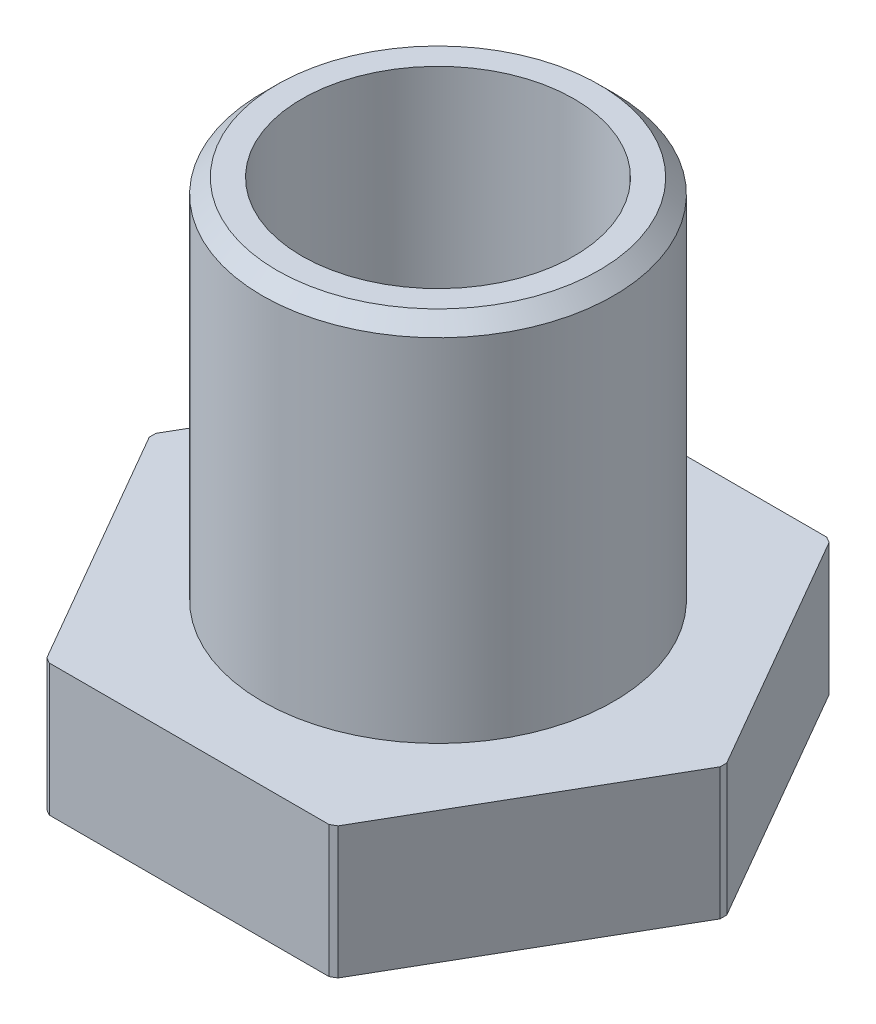
SolidWorks part; units mm, degrees
material "PA Тип 6"
ref_plane "Спереди" through (0, 0, 0) normal (0, 0, 1) x (1, 0, 0)
ref_plane "Сверху" through (0, 0, 0) normal (0, 1, 0) x (1, 0, 0)
ref_plane "Справа" through (0, 0, 0) normal (1, 0, 0) x (0, 0, -1)
sketch "Эскиз1" plane through (0, 0, 0) normal (0, 1, 0) x (1, 0, 0)
  line L1 (9.815, 0) -> (4.9075, 8.5)
  line L2 (4.9075, 8.5) -> (-4.9075, 8.5)
  line L3 (-4.9075, 8.5) -> (-9.815, 0)
  line L4 (-9.815, 0) -> (-4.9075, -8.5)
  line L5 (-4.9075, -8.5) -> (4.9075, -8.5)
  line L6 (4.9075, -8.5) -> (9.815, 0)
  circle A0 centre (0, 0) radius 8.5 construction
  circle A1 centre (0, 0) radius 4.65
  dimension "D2" = 9.3
  dimension "D1" = 17
extrude "Бобышка-Вытянуть1" add sketch "Эскиз1" along normal blind 17
sketch "Эскиз2" plane through (0, 17, 0) normal (0, 1, 0) x (1, 0, 0)
  circle A0 centre (0, 0) radius 6
  line M1 (4.9075, -8.5) -> (9.815, 0)
  line M2 (9.815, 0) -> (4.9075, 8.5)
  line M3 (4.9075, 8.5) -> (-4.9075, 8.5)
  line M4 (-4.9075, 8.5) -> (-9.815, 0)
  line M5 (-9.815, 0) -> (-4.9075, -8.5)
  line M6 (-4.9075, -8.5) -> (4.9075, -8.5)
  dimension "D1" = 12
extrude "Вырез-Вытянуть1" cut sketch "Эскиз2" against normal blind 12.5 contours A0 M6 M1 M2 M3 M4 M5
cosmetic thread "Условное изображение резьбы1" parameters "D1"=11.5, "D2"=10.619
sketch "Эскиз3" plane through (0, 0, 0) normal (0, -1, 0) x (1, 0, 0)
  circle A0 centre (0, 0) radius 6.75
  circle M7 centre (0, 0) radius 4.65
  dimension "D1" = 13.5
extrude "Вырез-Вытянуть2" cut sketch "Эскиз3" against normal blind 2.2 contours A0 M7
chamfer "Фаска1" distance 0.5 angle 45 1 edges at (0, 17, 6)
sketch "Эскиз4" plane through (0, 0, 0) normal (0, -1, 0) x (1, 0, 0)
  circle A0 centre (0, 0) radius 9.75
  line M2 (9.815, 0) -> (4.9075, 8.5)
  line M3 (4.9075, 8.5) -> (-4.9075, 8.5)
  line M4 (-4.9075, 8.5) -> (-9.815, 0)
  line M5 (-9.815, 0) -> (-4.9075, -8.5)
  line M6 (-4.9075, -8.5) -> (4.9075, -8.5)
  line M7 (4.9075, -8.5) -> (9.815, 0)
  dimension "D1" = 19.5
extrude "Вырез-Вытянуть3" cut sketch "Эскиз4" against normal through all contours A0 M4 M5 | A0 M3 M4 | A0 M2 M3 | A0 M7 M2 | A0 M6 M7 | A0 M5 M6
